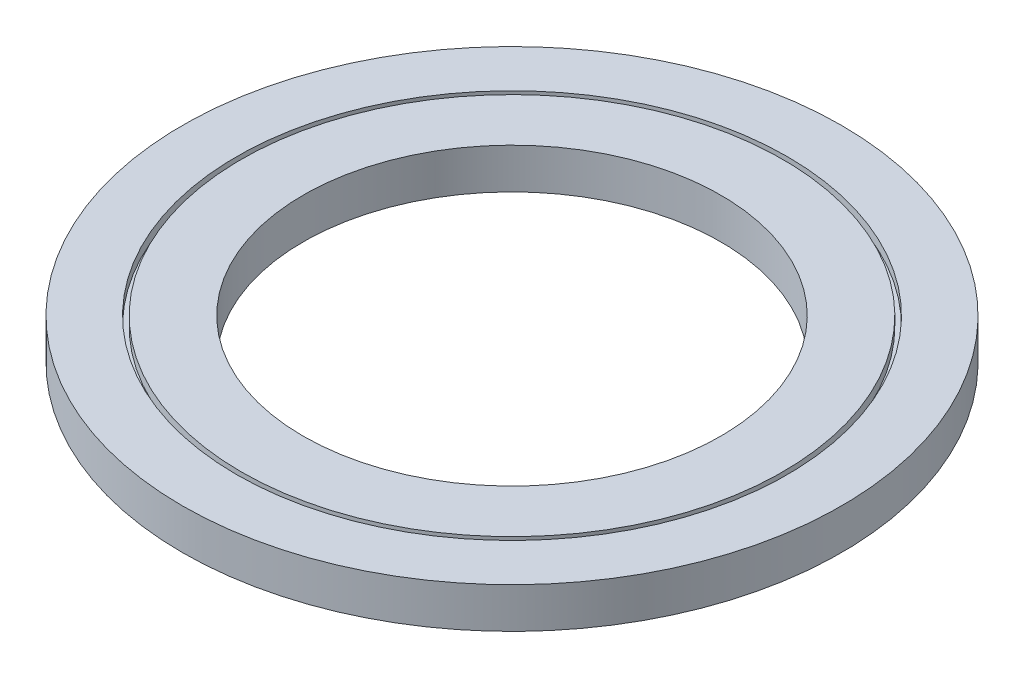
SolidWorks part; units mm, degrees
ref_plane "Front Plane" through (0, 0, 0) normal (0, 0, 1) x (1, 0, 0)
ref_plane "Top Plane" through (0, 0, 0) normal (0, 1, 0) x (1, 0, 0)
ref_plane "Right Plane" through (0, 0, 0) normal (1, 0, 0) x (0, 0, -1)
sketch "Sketch1" plane through (0, 0, 0) normal (0, 1, 0) x (1, 0, 0)
  circle A0 centre (0, 0) radius 70
  circle A1 centre (0, 0) radius 44.35
  dimension "D1" = 140
  dimension "D2" = 88.7
extrude "Boss-Extrude1" add sketch "Sketch1" along normal blind 8.6
sketch "Sketch2" plane through (0, 8.6, 0) normal (0, 1, 0) x (1, 0, 0)
  circle A0 centre (0, 0) radius 70 construction
  circle A1 centre (0, 0) radius 58 construction
  circle A2 centre (0, 0) radius 70 construction
  circle A3 centre (0, 0) radius 58.5
  circle A4 centre (0, 0) radius 57.5
  dimension "D1" = 12
  dimension "D2" = 0.5
  dimension "D3" = 0.5
extrude "Cut-Extrude1" cut sketch "Sketch2" against normal blind 2
